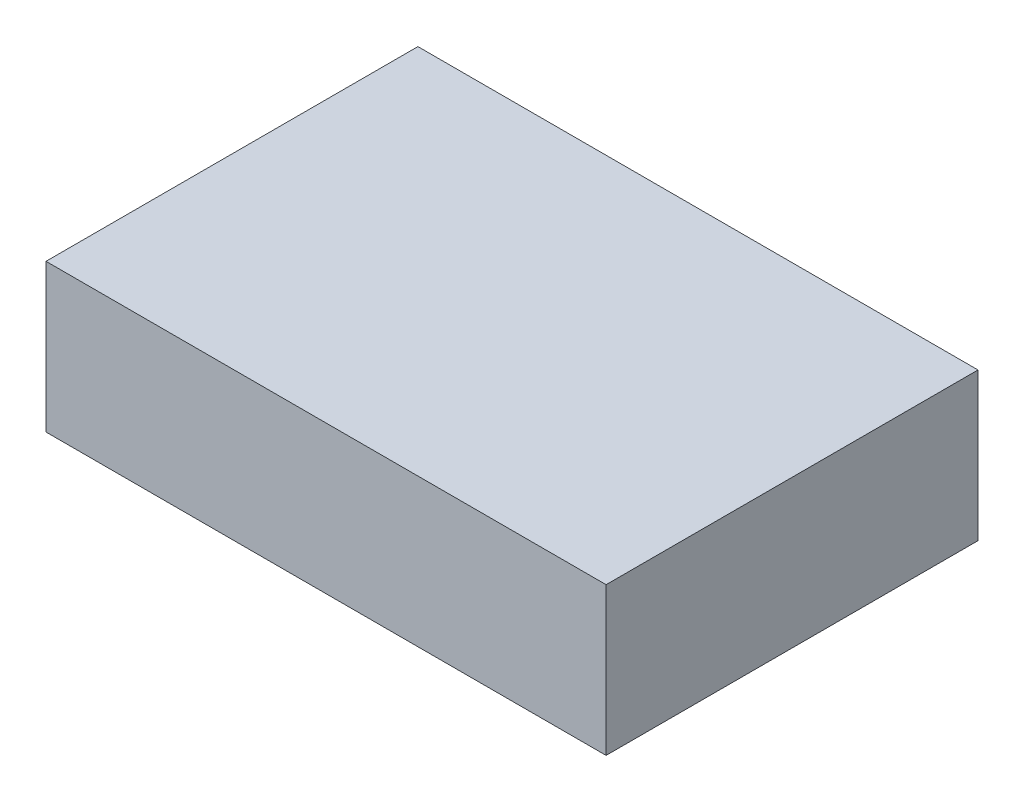
SolidWorks part; units mm, degrees
ref_plane "前视基准面" through (0, 0, 0) normal (0, 0, 1) x (1, 0, 0)
ref_plane "上视基准面" through (0, 0, 0) normal (0, 1, 0) x (1, 0, 0)
ref_plane "右视基准面" through (0, 0, 0) normal (1, 0, 0) x (0, 0, -1)
sketch "草图1" plane through (0, 0, 0) normal (0, 1, 0) x (1, 0, 0)
  line L1 (-62.5, -41.5) -> (62.5, -41.5)
  line L2 (-62.5, -41.5) -> (-62.5, 41.5)
  line L3 (-62.5, 41.5) -> (62.5, 41.5)
  line L4 (62.5, -41.5) -> (62.5, 41.5)
  line L5 (-62.5, -41.5) -> (62.5, 41.5) construction
  line L6 (-62.5, 41.5) -> (62.5, -41.5) construction
  point P0 (0, 0)
  dimension "D1" = 125
  dimension "D2" = 83
extrude "凸台-拉伸1" add sketch "草图1" along normal blind 33
